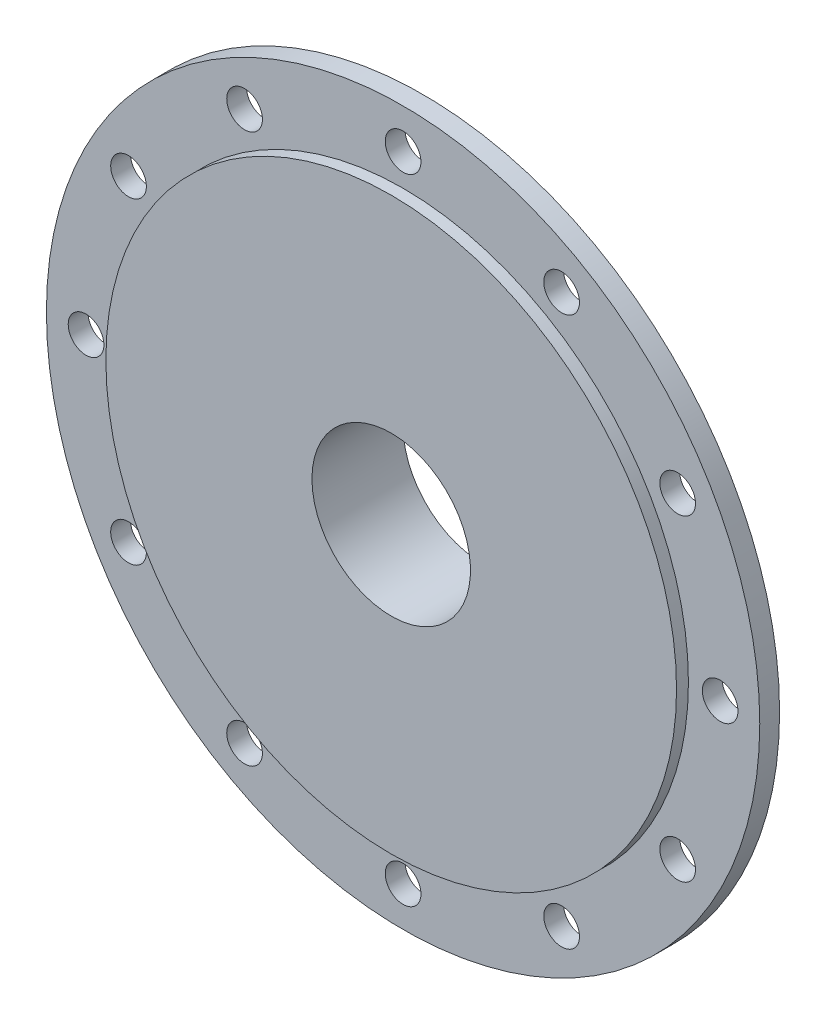
SolidWorks part; units mm, degrees
material "1060 Alaşım"
ref_plane "Ön Düzlem" through (0, 0, 0) normal (0, 0, 1) x (1, 0, 0)
ref_plane "Üst Düzlem" through (0, 0, 0) normal (0, 1, 0) x (1, 0, 0)
ref_plane "Sağ Düzlem" through (0, 0, 0) normal (1, 0, 0) x (0, 0, -1)
sketch "Çizim1" plane through (0, 0, 0) normal (1, 0, 0) x (0, 0, -1)
  line L0 (0, 0) -> (-55.1249, 0) construction
  line L1 (0, 0) -> (0, 20) construction
  line L2 (0, 20) -> (0, 72)
  line L3 (0, 72) -> (3, 72)
  line L4 (3, 72) -> (3, 90)
  line L5 (3, 90) -> (8, 90)
  line L6 (8, 90) -> (8, 67.5)
  line L7 (8, 67.5) -> (5, 67.5)
  line L8 (0, 0) -> (0, 25) construction
  line L9 (5, 67.5) -> (5, 25)
  line L10 (5, 25) -> (23, 25)
  line L11 (23, 25) -> (23, 0)
  line L13 (0, 0) -> (0, 20)
  line L14 (23, 0) -> (0, 0) construction
  line L15 (0, 0) -> (23, 0)
  dimension "D1" = 20
  dimension "D2" = 52
  dimension "D3" = 3
  dimension "D4" = 18
  dimension "D5" = 5
  dimension "D6" = 22.5
  dimension "D7" = 3
  dimension "D8" = 25
  dimension "D9" = 18
  dimension "D10" = 25
revolve "Döndür1" add sketch "Çizim1" angle 360 about L0
sketch "Çizim2" plane through (0, 0, -23) normal (0, 0, -1) x (-1, 0, 0)
  circle A0 centre (0, 0) radius 20
  dimension "D1" = 40
extrude "Kes-Ekstrüzyon1" cut sketch "Çizim2" against normal through all
sketch "Çizim3" plane through (0, 0, 0) normal (1, 0, 0) x (0, 0, -1)
  line L0 (23, 23) -> (8, 67.5)
  line L2 (23, -25) -> (23, 25) construction
  line L3 (23, -25) -> (23, 23) construction
  line L4 (23, 25) -> (5, 25) construction
  line L5 (23, 25) -> (5, 25) construction
  line L6 (8, -90) -> (8, 90) construction
  line L7 (8, -90) -> (8, 90) construction
  point P11 (23, 22.6565)
  dimension "D1" = 2
rib "Feder6" sketch "Çizim3" sketch "Çizim3" thickness 5 extrusion direction parallel to sketch draft on no parameters "D1"=5
mirror "Aynalama1" about plane through (0, 0, 0) normal (0, 1, 0) of "Feder6"
sketch "Çizim4" plane through (0, 0, 0) normal (0, 1, 0) x (1, 0, 0)
  line L0 (-23, 23) -> (-67.5, 8)
  line L1 (25, 23) -> (-25, 23) construction
  point P4 (-25, 23)
  point P5 (-25, 23)
  point P6 (0, 0)
  point P7 (-19.514, 23)
  dimension "D1" = 2
rib "Feder7" sketch "Çizim4" sketch "Çizim4" thickness 5 extrusion direction parallel to sketch draft on no parameters "D1"=5
mirror "Aynalama2" about plane through (0, 0, 0) normal (1, 0, 0) of "Feder7"
sketch "Çizim5" plane through (0, 0, -8) normal (0, 0, -1) x (-1, 0, 0)
  line L0 (0, 0) -> (0, 80) construction
  circle A0 centre (0, 0) radius 80 construction
  circle A1 centre (0, 80) radius 4.5
  circle A2 centre (40, 69.282) radius 4.5
  circle A3 centre (69.282, 40) radius 4.5
  circle A4 centre (80, 0) radius 4.5
  circle A5 centre (69.282, -40) radius 4.5
  circle A6 centre (40, -69.282) radius 4.5
  circle A7 centre (0, -80) radius 4.5
  circle A8 centre (-40, -69.282) radius 4.5
  circle A9 centre (-69.282, -40) radius 4.5
  circle A10 centre (-80, 0) radius 4.5
  circle A11 centre (-69.282, 40) radius 4.5
  circle A12 centre (-40, 69.282) radius 4.5
  point P30 (0, 0)
  dimension "D1" = 160
  dimension "D2" = 9
  dimension "D4" = 160
  dimension "D3" = 12
extrude "Kes-Ekstrüzyon2" cut sketch "Çizim5" against normal up to next
